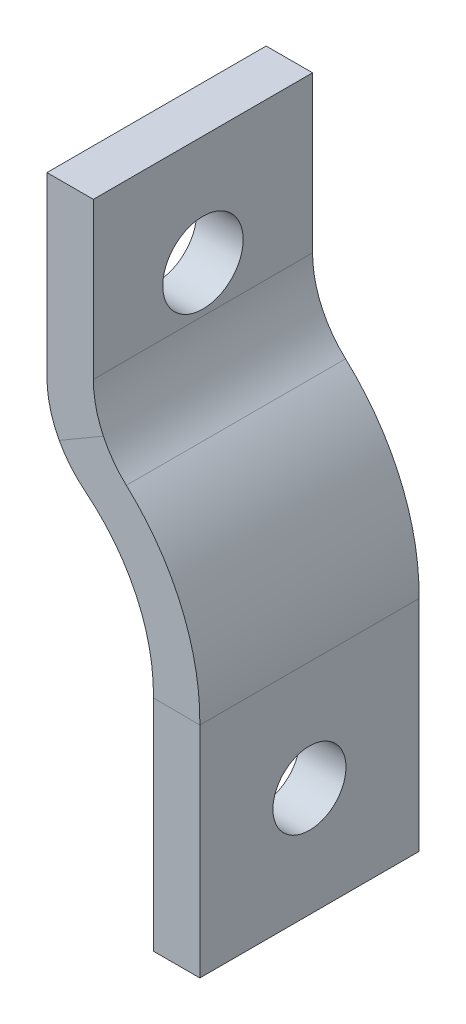
SolidWorks part; units mm, degrees
ref_plane "Front Plane" through (0, 0, 0) normal (0, 0, 1) x (1, 0, 0)
ref_plane "Top Plane" through (0, 0, 0) normal (0, 1, 0) x (1, 0, 0)
ref_plane "Right Plane" through (0, 0, 0) normal (1, 0, 0) x (0, 0, -1)
sketch "Sketch1" plane through (0, 0, 0) normal (0, 0, 1) x (1, 0, 0)
  line L0 (-14.2875, 7.5) -> (-14.2875, -7.5)
  line L1 (-7, -20) -> (-7, -35)
  circle A0 centre (0, 0) radius 12.7 construction
  arc A1 (-14.2875, -7.5) -> (-7, -20) centre (-20.9984, -19.7867) cw
  point P3 (-12.7, 0)
  point P4 (0, -12.7)
  dimension "D1" = 25.4
  dimension "D6" = 14
  dimension "D2" = 15
  dimension "D3" = 15
  dimension "D4" = 7
  dimension "D5" = 1.5875
  dimension "D7" = 20
  dimension "D8" = 7.5
sketch "Sketch2" plane through (0, 0, 0) normal (0, 1, 0) x (1, 0, 0)
  line L0 (-14.2875, 0) -> (-6.9984, 0) construction
  line L1 (-12.7, -7.5) -> (-15.875, -7.5)
  line L2 (-12.7, -7.5) -> (-12.7, 7.5)
  line L3 (-12.7, 7.5) -> (-15.875, 7.5)
  line L4 (-15.875, -7.5) -> (-15.875, 7.5)
  line L5 (-12.7, -7.5) -> (-15.875, 7.5) construction
  line L6 (-12.7, 7.5) -> (-15.875, -7.5) construction
  point P0 (-14.2875, 0)
  dimension "D1" = 15
  dimension "D2" = 3.175
sweep "Sweep1" add profiles "Sketch2" path "Sketch1"
fillet "Fillet1" radius 7 2 edges at (-15.875, -8.4418, 0) (-12.7, -6.5918, 0)
sketch "Sketch3" plane through (-8.5875, 0, 0) normal (-1, 0, 0) x (0, 0, 1)
  line L0 (0, -20) -> (0, -35) construction
  circle A0 centre (0, -27.5) radius 2.5
  dimension "D1" = 5
hole_wizard "M5 Clearance Hole1" positions "Sketch4" profile "Sketch5" hole size "M5" standard "AS" end condition through all
sketch "Sketch4" plane through (-15.875, 0, 0) normal (-1, 0, 0) x (0, 0, 1)
  point P0 (0, 0)
sketch "Sketch5" plane through (-15.875, 0, 0) normal (0, 1, 0) x (0, 0, 1)
  line L0 (0, 0) -> (0, 10.4641)
  line L1 (0, 10.4641) -> (2.75, 10.4641)
  line L2 (2.75, 10.4641) -> (2.75, 0)
  line L5 (2.75, 0) -> (0, 0)
  line L11 (0, -6.35) -> (0, 107.95) construction
  dimension "Thru Hole Dia." = 5.5
  dimension "Thru Hole Depth" = 10.4641
extrude "Cut-Extrude1" cut sketch "Sketch3" against normal through all both and the other way through all
equation "\"keelOutDiameter\"= 1in"
equation "\"keelInDiameter\"= \"keelOutDiameter\" - 0.125in"
equation "\"frontBoltClearance\"= 7.25mm"
equation "\"betweenBoltsDistance\"= 20mm"
equation "\"wingLength\"= 1.4m"
equation "\"frontTubeLength\"= \"wingLength\" / sin ( 34.95deg )"
equation "\"plateThickness\"= 5mm"
equation "\"crossBarOutDiameter\"= 1in"
equation "\"crossBarInDiameter\"= \"crossBarOutDiameter\" - 0.125in"
equation "\"frontToCrossBar\"= 466mm"
equation "\"cablePinDiameter\"= 5mm"
equation "\"D2@Sketch1\"=\"cablePinDiameter\"*3"
equation "\"D1@Sketch2\"=\"cablePinDiameter\"*3"
equation "\"D1@Sketch3\"=\"cablePinDiameter\""
